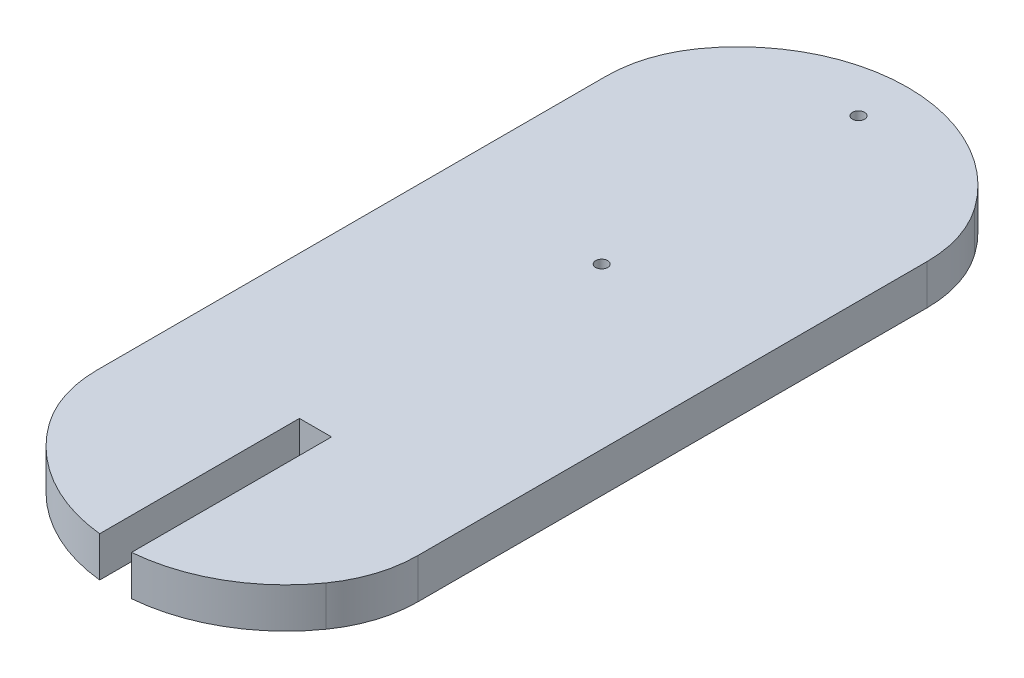
SolidWorks part; units mm, degrees
ref_plane "Front Plane" through (0, 0, 0) normal (0, 0, 1) x (1, 0, 0)
ref_plane "Top Plane" through (0, 0, 0) normal (0, 1, 0) x (1, 0, 0)
ref_plane "Right Plane" through (0, 0, 0) normal (1, 0, 0) x (0, 0, -1)
sketch "Sketch2" plane through (0, 0, 0) normal (0, 1, 0) x (1, 0, 0)
  line L1 (-20, -35) -> (20, -35)
  line L2 (-20, -35) -> (-20, 35)
  line L3 (-20, 35) -> (20, 35)
  line L4 (20, -35) -> (20, 35)
  line L5 (-20, -35) -> (20, 35) construction
  line L6 (-20, 35) -> (20, -35) construction
  arc A0 (-20, 35) -> (20, 35) centre (0, 28.172) cw
  arc A1 (-20, -35) -> (20, -35) centre (0, -28.1826) ccw
  point P0 (0, 0)
  dimension "D3" = 21.1334
  dimension "D4" = 21.13
  dimension "D1" = 40
  dimension "D2" = 70
extrude "Boss-Extrude1" add sketch "Sketch2" along normal blind 5 contours L1 A1 | L1 L4 L3 L2 | A0 L3
fillet "Fillet1" radius 15 4 edges at (20, 2.5, 35) (-20, 2.5, 35) (-20, 2.5, -35) (20, 2.5, -35)
sketch "Sketch3" plane through (0, 0, 0) normal (0, -1, 0) x (1, 0, 0)
  line L0 (0, -49.3055) -> (0, 49.3126) construction
  line L1 (0, 49.3126) -> (1.8237, 49.3126)
  line L2 (1.8237, 49.3126) -> (1.8237, 24.3126)
  line L3 (1.8237, 24.3126) -> (-2.1763, 24.3126)
  line L4 (-2.1763, 24.3126) -> (-2.1763, 49.3126)
  line L5 (-2.1763, 49.3126) -> (0, 49.3126)
  line L6 (20, 31.729) -> (20, -31.7243) construction
  arc A0 (-17.2281, -40.4119) -> (17.2281, -40.4119) centre (0, -28.172) ccw construction
  arc A1 (17.2349, 40.407) -> (-17.2349, 40.407) centre (0, 28.1826) ccw construction
  dimension "D1" = 4
  dimension "D2" = 25
  dimension "D3" = 18.1763
extrude "Cut-Extrude1" cut sketch "Sketch3" against normal through all
sketch "Sketch4" plane through (0, 0, 0) normal (0, -1, 0) x (1, 0, 0)
  line L0 (20, 31.729) -> (20, -31.7243) construction
  line L1 (-20, 31.729) -> (-20, -31.7243) construction
  circle A1 centre (0, -43.172) radius 0.75
  circle A3 centre (0, -11.172) radius 0.75
  arc A4 (-17.2281, -40.4119) -> (17.2281, -40.4119) centre (0, -28.172) ccw construction
  dimension "D1" = 1.5
  dimension "D2" = 15
  dimension "D3" = 1.5
  dimension "D4" = 32
  dimension "D5" = 20
  dimension "D6" = 20
extrude "Cut-Extrude2" cut sketch "Sketch4" against normal through all
